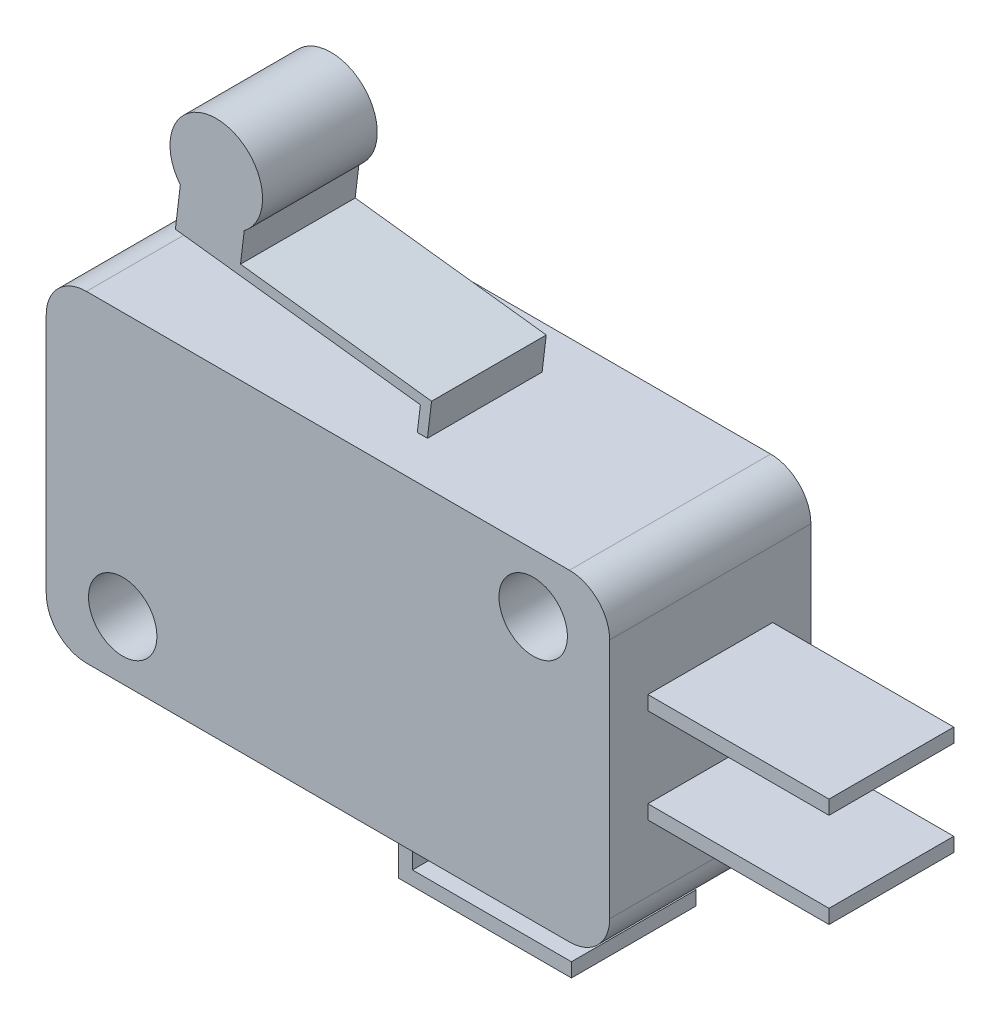
SolidWorks part; units mm, degrees
ref_plane "Front Plane" through (0, 0, 0) normal (0, 0, 1) x (1, 0, 0)
ref_plane "Top Plane" through (0, 0, 0) normal (0, 1, 0) x (1, 0, 0)
ref_plane "Right Plane" through (0, 0, 0) normal (1, 0, 0) x (0, 0, -1)
sketch "Sketch1" plane through (0, 0, 0) normal (0, 0, 1) x (1, 0, 0)
  line L0 (2, 2) -> (26, 14) construction
  line L1 (2, 0) -> (26, 0)
  line L2 (0, 2) -> (0, 14)
  line L3 (2, 16) -> (26, 16)
  line L4 (28, 2) -> (28, 14)
  line L5 (3.8, 4.6) -> (3.8, 1.2) construction
  line L6 (14, 8) -> (11.798, 12.4039) construction
  arc A0 (26, 0) -> (28, 2) centre (26, 2) ccw
  arc A1 (2, 0) -> (0, 2) centre (2, 2) cw
  arc A2 (26, 16) -> (28, 14) centre (26, 14) cw
  arc A3 (0, 14) -> (2, 16) centre (2, 14) cw
  circle A4 centre (3.8, 2.9) radius 1.7
  circle A5 centre (24.2, 13.1) radius 1.7
  point P7 (28, 0)
  point P10 (0, 0)
  point P13 (28, 16)
  dimension "D3" = 2
  dimension "D4" = 3.4
  dimension "D1" = 28
  dimension "D2" = 16
  dimension "D5" = 1.2
extrude "Boss-Extrude1" add sketch "Sketch1" along normal mid plane 10
sketch "Sketch2" plane through (0, 0, 0) normal (0, 0, 1) x (1, 0, 0)
  line L0 (15.919, 12.9234) -> (16.4436, 17.2636)
  line L1 (16.4436, 17.2636) -> (4.2676, 18.7354)
  line L2 (4.2676, 18.7354) -> (4.5133, 20.7683)
  line L3 (4.7038, 22.3445) -> (7.8807, 21.9606) construction
  line L4 (7.6902, 20.3843) -> (7.5044, 18.8477)
  line L5 (7.5044, 18.8477) -> (17, 17.7)
  line L6 (17, 17.7) -> (16.4154, 12.8634)
  line L7 (16.4154, 12.8634) -> (15.919, 12.9234)
  line L8 (6.2923, 22.1525) -> (5.856, 18.5434) construction
  line L9 (6.2923, 22.1525) -> (6.576, 24.5) construction
  line L10 (6.576, 24.5) -> (3.0154, 24.9304) construction
  line L11 (2, 0) -> (26, 0) construction
  line L12 (0, 14) -> (0, 2) construction
  line L13 (4, 22.2166) -> (4, 15.7748) construction
  line L14 (28, 2) -> (28, 14) construction
  circle A0 centre (6.3, 22.2166) radius 2.3
  dimension "D3" = 4.6
  dimension "D7" = 24.5
  dimension "D1" = 0.5
  dimension "D2" = 0.5
  dimension "D4" = 6
  dimension "D5" = 17.7
  dimension "D6" = 17
  dimension "D8" = 24
  dimension "D9" = 3.2
extrude "Boss-Extrude2" add sketch "Sketch2" along normal mid plane 5.7 contours A0 L2 L1 L0 L7 L6 L5 L4 | A0
sketch "Sketch3" plane through (0, 0, 0) normal (0, 0, 1) x (1, 0, 0)
  line L0 (28, 10.7) -> (37, 10.7)
  line L1 (28, 2) -> (28, 14) construction
  line L2 (37, 10.7) -> (37, 10)
  line L3 (37, 10) -> (28, 10)
  line L4 (28, 10) -> (28, 10.7)
  line L5 (28, 8) -> (43.0344, 8) construction
  line L6 (28, 6) -> (28, 5.3)
  line L7 (37, 6) -> (28, 6)
  line L8 (37, 5.3) -> (37, 6)
  line L9 (28, 5.3) -> (37, 5.3)
  line L10 (26, 16) -> (2, 16) construction
  line L11 (15.6, 0) -> (15.6, -3.4)
  line L12 (2, 0) -> (26, 0) construction
  line L13 (15.6, -3.4) -> (24.2, -3.4)
  line L14 (24.2, -3.4) -> (24.2, -2.7)
  line L15 (24.2, -2.7) -> (16.3, -2.7)
  line L16 (16.3, -2.7) -> (16.3, 0)
  line L17 (15.6, 0) -> (16.3, 0)
  dimension "D1" = 0.7
  dimension "D2" = 9
  dimension "D3" = 6
  dimension "D4" = 0.7
  dimension "D5" = 8.6
  dimension "D6" = 0.7
  dimension "D7" = 3.4
  dimension "D8" = 12.4
extrude "Boss-Extrude3" add sketch "Sketch3" along normal mid plane 6.2
sketch "Sketch4" plane through (0, 0, 0) normal (0, 0, 1) x (1, 0, 0)
  line L0 (4.2, 22) -> (4.2, 0) construction
  line L1 (2, 0) -> (26, 0) construction
  line L2 (6.5, 19.7) -> (1.9, 19.7) construction
  line L3 (0, 14) -> (0, 2) construction
  line L4 (14, 16) -> (14, 0) construction
  line L5 (26, 16) -> (2, 16) construction
  line L6 (4.2, 19.7) -> (23.8, 19.7)
  circle A0 centre (4.2, 19.7) radius 2.3
  circle A1 centre (14, 8) radius 15.262
  dimension "D2" = 4.6
  dimension "D1" = 22
  dimension "D3" = 6.5
ref_plane "Plane1" through (14, 0, 0) normal (1, 0, 0) x (0, 0, -1)
